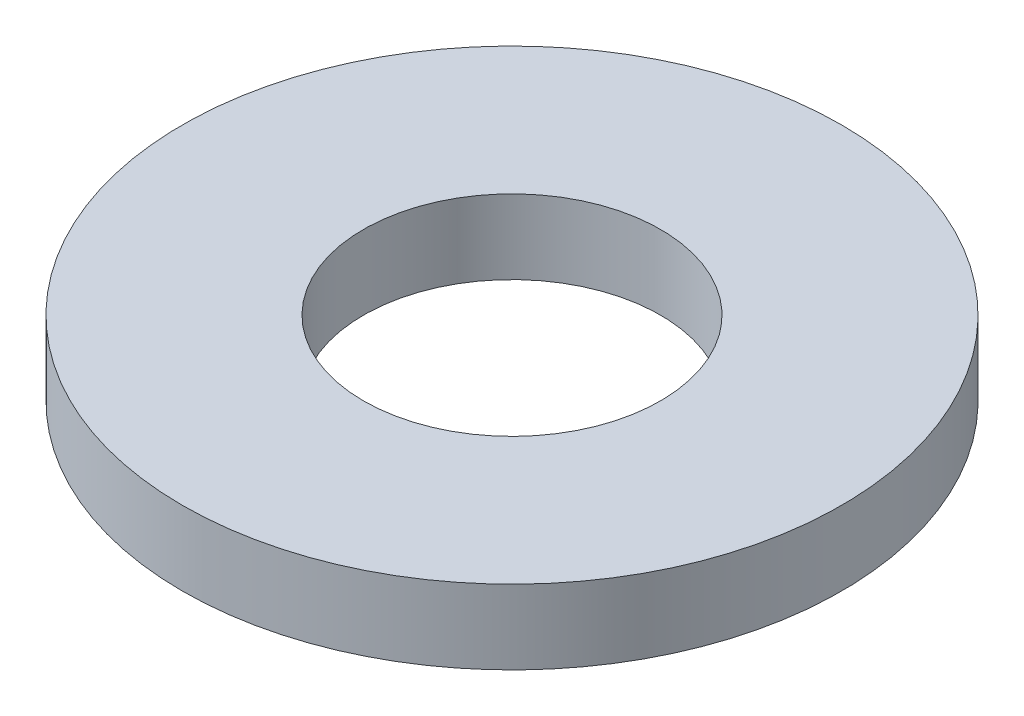
SolidWorks part; units mm, degrees
ref_plane "Front Plane" through (0, 0, 0) normal (0, 0, 1) x (1, 0, 0)
ref_plane "Top Plane" through (0, 0, 0) normal (0, 1, 0) x (1, 0, 0)
ref_plane "Right Plane" through (0, 0, 0) normal (1, 0, 0) x (0, 0, -1)
sketch "Sketch1" plane through (0, 0, 0) normal (0, 1, 0) x (1, 0, 0)
  circle A0 centre (0, 0) radius 4
  circle A1 centre (0, 0) radius 8.875
  dimension "D1" = 8
  dimension "D2" = 17.75
extrude "Boss-Extrude1" add sketch "Sketch1" along normal blind 2
